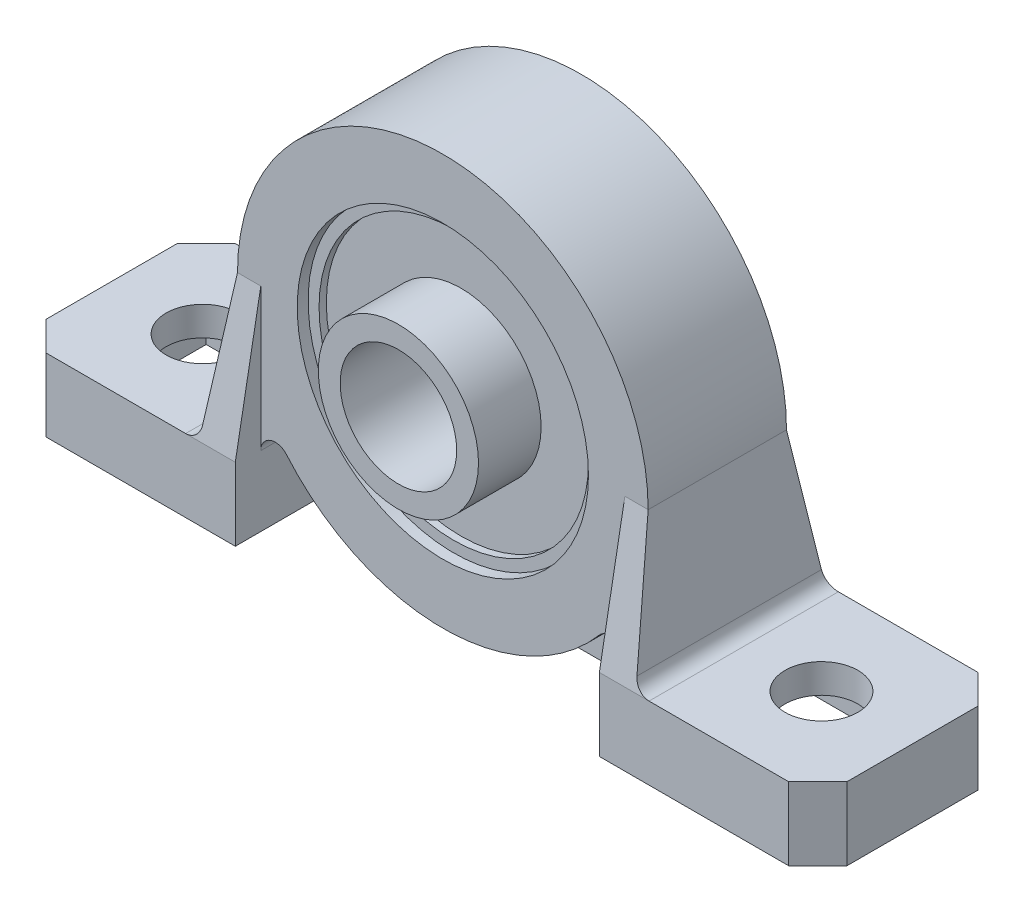
SolidWorks part; units mm, degrees
ref_plane "Front Plane" through (0, 0, 0) normal (0, 0, 1) x (1, 0, 0)
ref_plane "Top Plane" through (0, 0, 0) normal (0, 1, 0) x (1, 0, 0)
ref_plane "Right Plane" through (0, 0, 0) normal (1, 0, 0) x (0, 0, -1)
sketch "Sketch1" plane through (0, 0, 0) normal (0, 0, 1) x (1, 0, 0)
  circle A0 centre (0, 0) radius 10
  dimension "D1" = 20
extrude "Boss-Extrude1" add sketch "Sketch1" along normal mid plane 8
sketch "Sketch2" plane through (0, 0, 4) normal (0, 0, 1) x (1, 0, 0)
  circle A2 centre (0, 0) radius 9.25
  circle A3 centre (0, 0) radius 9.25
  dimension "D1" = 0.75
extrude "Cut-Extrude2" cut sketch "Sketch2" against normal blind 0.5
mirror "Mirror1" about plane through (0, 0, 0) normal (0, 0, 1) of "Cut-Extrude2"
sketch "Sketch6" plane through (0, 0, 0) normal (0, 0, 1) x (1, 0, 0)
  line L0 (14.1, 0) -> (15, -9.6)
  line L1 (15, -9.6) -> (27.5, -9.6)
  line L2 (27.5, -9.6) -> (27.5, -14.6)
  line L3 (27.5, -14.6) -> (12.5, -14.6)
  line L4 (12.5, -14.6) -> (12.5, -14.1)
  line L5 (12.5, -14.1) -> (-12.5, -14.1)
  line L6 (0, -4.675) -> (0, 4.675) construction
  line L7 (-12.5, -14.6) -> (-12.5, -14.1)
  line L8 (-27.5, -14.6) -> (-12.5, -14.6)
  line L9 (-27.5, -9.6) -> (-27.5, -14.6)
  line L10 (-15, -9.6) -> (-27.5, -9.6)
  line L11 (-14.1, 0) -> (-15, -9.6)
  circle A0 centre (0, 0) radius 14.1
  circle A3 centre (0, 0) radius 10
  circle A4 centre (0, 0) radius 10
  point P13 (0, -14.1)
  dimension "D1" = 28.2
  dimension "D2" = 5
  dimension "D3" = 12.5
  dimension "D4" = 0.5
  dimension "D5" = 25
  dimension "D6" = 55
  dimension "D7" = 0
extrude "Boss-Extrude4" add sketch "Sketch6" along normal mid plane 13 contours A0 A4 | A0 L11 L10 L9 L8 L7 L5 | A0 L5 L4 L3 L2 L1 L0
sketch "Sketch7" plane through (0, 0, 0) normal (1, 0, 0) x (0, 0, -1)
  line L0 (-6.5, -9.6) -> (-4.75, 0)
  line L1 (-6.5, 0) -> (6.5, 0) construction
  line L2 (-4.75, 0) -> (-4.75, 14.1)
  line L3 (6.5, 14.1) -> (-6.5, 14.1) construction
  line L4 (-4.75, 14.1) -> (4.75, 14.1)
  line L6 (-6.5, -9.6) -> (6.5, -9.6) construction
  line L7 (0, 15.785) -> (0, -15.785) construction
  line L8 (6.5, -9.6) -> (4.75, 0)
  line L9 (4.75, 0) -> (4.75, 14.1)
  line L10 (-6.5, -9.6) -> (-6.5, -14.6)
  line L11 (-6.5, -14.6) -> (6.5, -14.6)
  line L12 (6.5, -14.6) -> (6.5, -9.6)
  point P15 (0, -9.6)
  point P17 (0, 14.1)
  dimension "D1" = 9.5
extrude "Cut-Extrude6" cut sketch "Sketch7" against normal mid plane 57 flip side to cut
sketch "Sketch8" plane through (0, 0, 3.5) normal (0, 0, 1) x (1, 0, 0)
  circle A0 centre (0, 0) radius 4
  dimension "D1" = 8
extrude "Cut-Extrude7" cut sketch "Sketch8" against normal up to surface (7 mm away) up to face at (9.25, 0, -3.5)
sketch "Sketch11" plane through (0, -14.1, 0) normal (0, -1, 0) x (1, 0, 0)
  line L0 (12.5, 6.5) -> (12.5, -6.5) construction
  line L1 (-12.5, 6.5) -> (12.5, 6.5)
  line L2 (-12.5, 6.5) -> (-12.5, 4.75)
  line L3 (-12.5, 4.75) -> (12.5, 4.75)
  line L4 (12.5, 6.5) -> (12.5, 4.75)
  line L5 (15.785, 0) -> (-15.785, 0) construction
  line L6 (-12.5, -4.75) -> (12.5, -4.75)
  line L7 (12.5, -6.5) -> (12.5, -4.75)
  line L8 (-12.5, -6.5) -> (12.5, -6.5)
  line L9 (-12.5, -6.5) -> (-12.5, -4.75)
  dimension "D1" = 9.5
extrude "Cut-Extrude8" cut sketch "Sketch11" against normal through all
sketch "Sketch12" plane through (0, 0, 4.75) normal (0, 0, 1) x (1, 0, 0)
  line L2 (-12.5, -6.5238) -> (-12.5, -14.1)
  line L3 (-12.5, 0) -> (-12.5, -14.1) construction
  line L4 (-12.5, -14.6) -> (-12.5, -9.6) construction
  line L5 (-12.5, -14.1) -> (12.5, -14.1)
  line L6 (0, -7.15) -> (0, 7.15) construction
  line L7 (12.5, -6.5238) -> (12.5, -14.1)
  arc A0 (-12.5, -6.5238) -> (12.5, -6.5238) centre (0, 0) ccw
  line M6 (-12.5, 0) -> (-12.5, -14.1)
  line M7 (-12.5, -14.1) -> (12.5, -14.1)
  line M8 (12.5, -14.1) -> (12.5, 0)
extrude "Cut-Extrude9" cut sketch "Sketch12" against normal blind 3.5 contours A0 M6 M7 | A0 L5 M8
mirror "Mirror2" about plane through (0, 0, 0) normal (0, 0, 1) of "Cut-Extrude9"
sketch "Sketch9" plane through (0, 0, 3.5) normal (0, 0, 1) x (1, 0, 0)
  circle A0 centre (0, 0) radius 5.5
  circle A1 centre (0, 0) radius 4
  dimension "D1" = 11
  dimension "D2" = 8
extrude "Boss-Extrude5" add sketch "Sketch9" along normal blind 4.3
sketch "Sketch10" plane through (0, 0, -3.5) normal (0, 0, -1) x (-1, 0, 0)
  circle A0 centre (0, 0) radius 4
  circle A1 centre (0, 0) radius 5.5
  dimension "D1" = 8
  dimension "D2" = 11
extrude "Boss-Extrude6" add sketch "Sketch10" along normal blind 1
sketch "Sketch13" plane through (0, -14.6, 0) normal (0, -1, 0) x (1, 0, 0)
  line L4 (0, -7.865) -> (0, 7.865) construction
  line L5 (-14.5, 4.5) -> (-14.5, -4.5)
  line L6 (-25.5, 4.5) -> (-14.5, 4.5)
  line L7 (-25.5, -4.5) -> (-25.5, 4.5)
  line L8 (14.5, -4.5) -> (25.5, -4.5)
  line L9 (25.5, -4.5) -> (25.5, 4.5)
  line L10 (25.5, 4.5) -> (14.5, 4.5)
  line L11 (14.5, 4.5) -> (14.5, -4.5)
  line L12 (14.5, -4.5) -> (25.5, -4.5)
  line L13 (25.5, -4.5) -> (25.5, 4.5)
  line L14 (25.5, 4.5) -> (14.5, 4.5)
  line L15 (14.5, 4.5) -> (14.5, -4.5)
  line L16 (-14.5, -4.5) -> (-25.5, -4.5)
  dimension "D1" = 2
extrude "Cut-Extrude10" cut sketch "Sketch13" against normal blind 3
sketch "Sketch14" plane through (0, -11.6, 0) normal (0, -1, 0) x (1, 0, 0)
  line L0 (0, -7.865) -> (0, 7.865) construction
  circle A0 centre (21.25, 0) radius 2.5
  circle A1 centre (-21.25, 0) radius 2.5
  dimension "D2" = 5
  dimension "D1" = 42.5
extrude "Cut-Extrude11" cut sketch "Sketch14" against normal up to surface (2 mm away) up to face at (-21.25, -9.6, 0)
chamfer "Chamfer1" distance 2 angle 45 4 edges at (-27.5, -12.1, -6.5) (27.5, -12.1, 6.5) (-27.5, -12.1, 6.5) (27.5, -12.1, -6.5)
fillet "Fillet1" radius 1 6 edges at (12.5, -6.5238, -3) (-12.5, -6.5238, -3) (-12.5, -6.5238, 3) (12.5, -6.5238, 3) (-15, -9.6, 0) (15, -9.6, 0)
